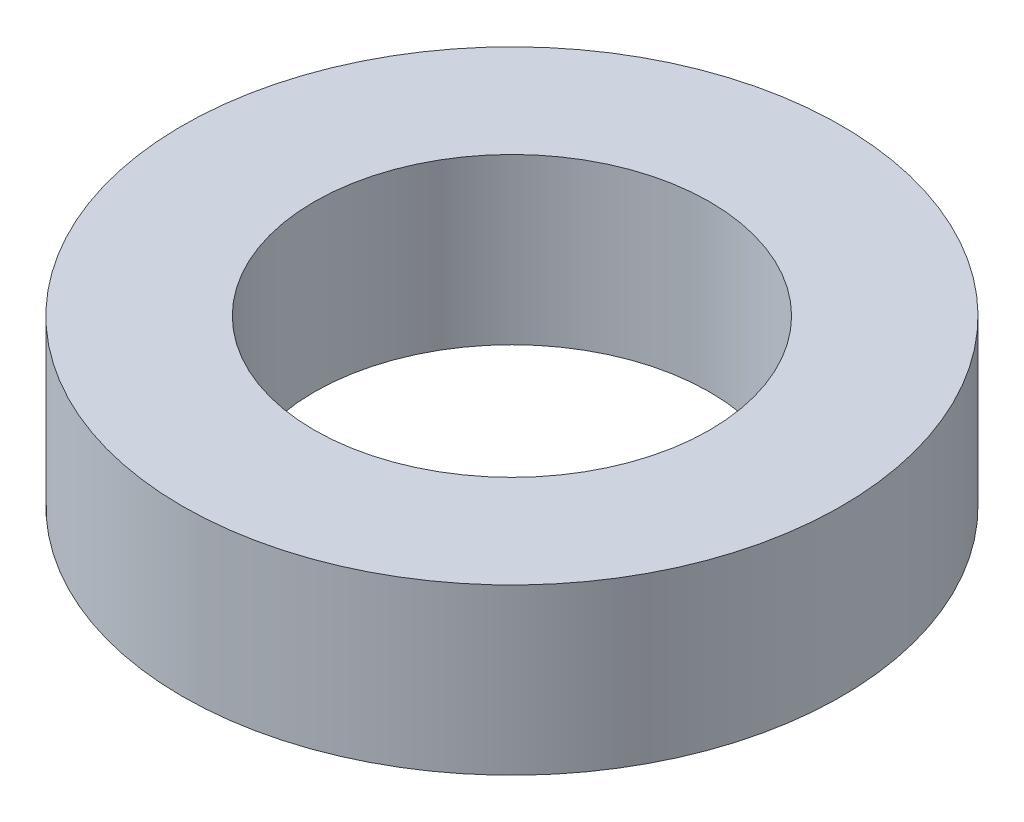
SolidWorks part; units mm, degrees
ref_plane "Front Plane" through (0, 0, 0) normal (0, 0, 1) x (1, 0, 0)
ref_plane "Top Plane" through (0, 0, 0) normal (0, 1, 0) x (1, 0, 0)
ref_plane "Right Plane" through (0, 0, 0) normal (1, 0, 0) x (0, 0, -1)
sketch "Sketch1" plane through (0, 0, 0) normal (0, 1, 0) x (1, 0, 0)
  circle A0 centre (0, 0) radius 6
  circle A1 centre (0, 0) radius 10
extrude "Boss-Extrude1" add sketch "Sketch1" along normal blind 5
